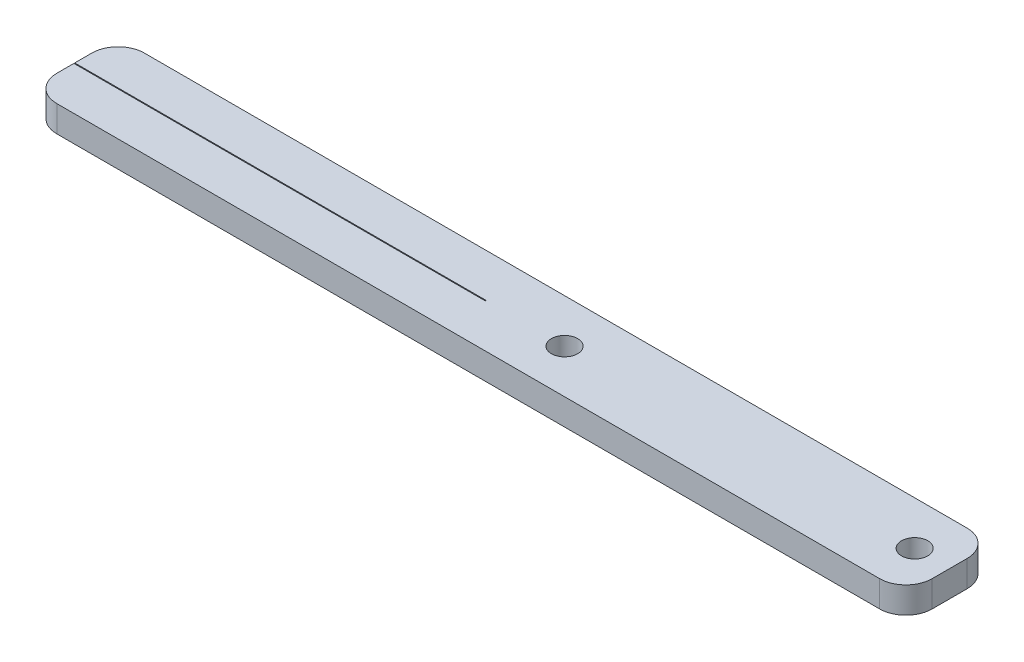
SolidWorks part; units mm, degrees
material "Acrylic (Medium-high impact)"
ref_plane "Front Plane" through (0, 0, 0) normal (0, 0, 1) x (1, 0, 0)
ref_plane "Top Plane" through (0, 0, 0) normal (0, 1, 0) x (1, 0, 0)
ref_plane "Right Plane" through (0, 0, 0) normal (1, 0, 0) x (0, 0, -1)
sketch "Sketch1" plane through (0, 0, 0) normal (0, 1, 0) x (1, 0, 0)
  line L1 (-50, 5) -> (50, 5)
  line L2 (-50, 5) -> (-50, -5)
  line L3 (-50, -5) -> (50, -5)
  line L4 (50, 5) -> (50, -5)
  line L5 (-50, 5) -> (50, -5) construction
  line L6 (-50, -5) -> (50, 5) construction
  point P0 (0, 0)
  dimension "D1" = 10
  dimension "D2" = 100
extrude "Boss-Extrude1" add sketch "Sketch1" along normal blind 3
sketch "Sketch2" plane through (0, 3, 0) normal (0, 1, 0) x (1, 0, 0)
  line L0 (26.3156, 5) -> (26.3156, -5) construction
  line L1 (-50, -5) -> (50, -5) construction
  line L2 (-50, 5) -> (-50, -5) construction
  line L4 (-3, 0.05) -> (-50, 0.05)
  line L5 (-3, 0.05) -> (-3, -0.05)
  line L6 (-3, -0.05) -> (-50, -0.05)
  line L7 (-50, 0.05) -> (-50, -0.05)
  line L8 (-3, 0.05) -> (-50, -0.05) construction
  line L9 (-3, -0.05) -> (-50, 0.05) construction
  point P0 (-26.5, 0)
  point P10 (26.3156, 0)
  point P14 (-50, 0)
  dimension "D1" = 47
  dimension "D2" = 0.1
fillet "Fillet1" radius 3 4 edges at (50, 1.5, 5) (50, 1.5, -5) (-50, 1.5, -5) (-50, 1.5, 5)
hole_wizard "Ø3.0mm Dowel Hole1" positions "Sketch3" profile "Sketch5" hole size "Ø3.0" standard "ISO" end condition through all
sketch "Sketch3" plane through (0, 3, 0) normal (0, 1, 0) x (1, 0, 0)
  line L0 (50, -2) -> (50, 2) construction
  point P0 (46, 0)
  point P5 (6, 0)
  dimension "D1" = 40
  dimension "D2" = 4
sketch "Sketch5" plane through (46, 3, 0) normal (1, 0, 0) x (0, 0, 1)
  line L0 (0, 0) -> (0, 3)
  line L1 (0, 3) -> (1.5, 3)
  line L2 (1.5, 3) -> (1.5, 0)
  line L5 (1.5, 0) -> (0, 0)
  line L11 (0, -22.0399) -> (0, 107.95) construction
  dimension "Thru Hole Dia." = 3
  dimension "Thru Hole Depth" = 3
extrude "Cut-Extrude1" cut sketch "Sketch2" against normal blind 10
